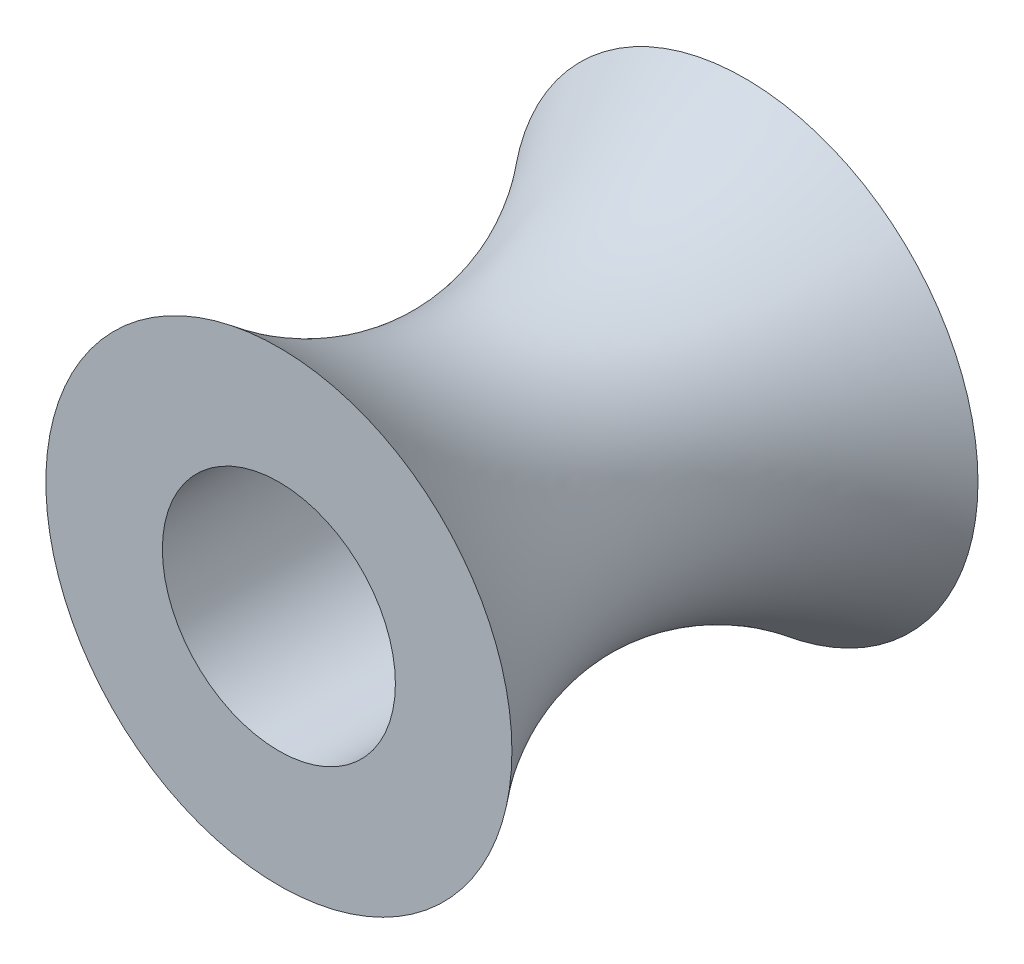
SolidWorks part; units mm, degrees
ref_plane "Front Plane" through (0, 0, 0) normal (0, 0, 1) x (1, 0, 0)
ref_plane "Top Plane" through (0, 0, 0) normal (0, 1, 0) x (1, 0, 0)
ref_plane "Right Plane" through (0, 0, 0) normal (1, 0, 0) x (0, 0, -1)
sketch "Sketch1" plane through (0, 0, 0) normal (0, 0, 1) x (1, 0, 0)
  circle A0 centre (0, 0) radius 5
  dimension "D1" = 10
extrude "Boss-Extrude1" add sketch "Sketch1" along normal blind 10
sketch "Sketch2" plane through (0, 0, 0) normal (1, 0, 0) x (0, 0, -1)
  line L0 (0, 5) -> (-10, 5) construction
  line L1 (-13.9703, 0) -> (1.2464, 0) construction
  line L2 (-10, 5) -> (0, 5)
  spline S0 degree 2 poles (-10, 5) (-4.983, 0.9996) (0, 5) knots 0 0 0 1 1 1
  dimension "D1" = 2
revolve "Cut-Revolve1" cut sketch "Sketch2" angle 360 about L1
sketch "Sketch3" plane through (0, 0, 10) normal (0, 0, 1) x (1, 0, 0)
  circle A0 centre (0, 0) radius 2.5
  dimension "D1" = 5
extrude "Cut-Extrude1" cut sketch "Sketch3" against normal through all
